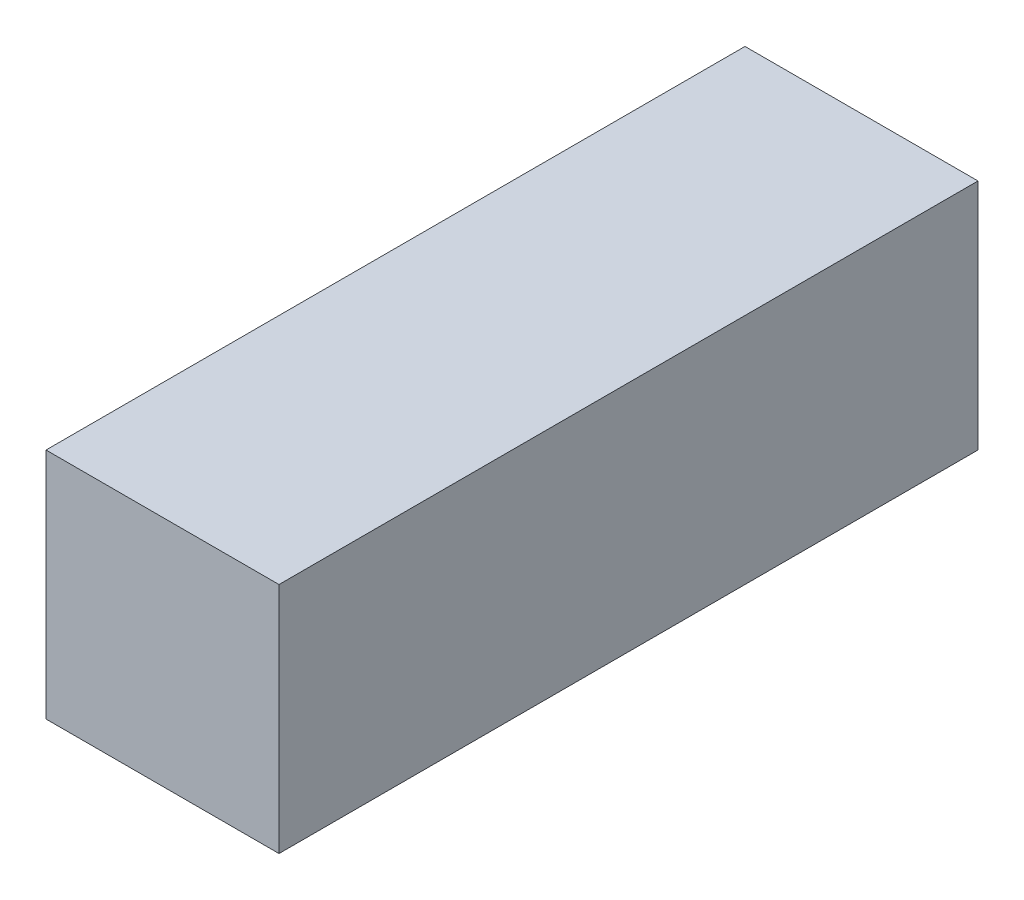
SolidWorks part; units mm, degrees
material "Polyurethane Foam Flexible"
ref_plane "Front Plane" through (0, 0, 0) normal (0, 0, 1) x (1, 0, 0)
ref_plane "Top Plane" through (0, 0, 0) normal (0, 1, 0) x (1, 0, 0)
ref_plane "Right Plane" through (0, 0, 0) normal (1, 0, 0) x (0, 0, -1)
sketch "Sketch1" plane through (0, 0, 0) normal (0, 1, 0) x (1, 0, 0)
  line L1 (0, 0) -> (101.6, 0)
  line L2 (0, 0) -> (0, 304.8)
  line L3 (0, 304.8) -> (101.6, 304.8)
  line L4 (101.6, 0) -> (101.6, 304.8)
  dimension "D1" = 101.6
  dimension "D2" = 304.8
extrude "Boss-Extrude1" add sketch "Sketch1" along normal blind 101.6
